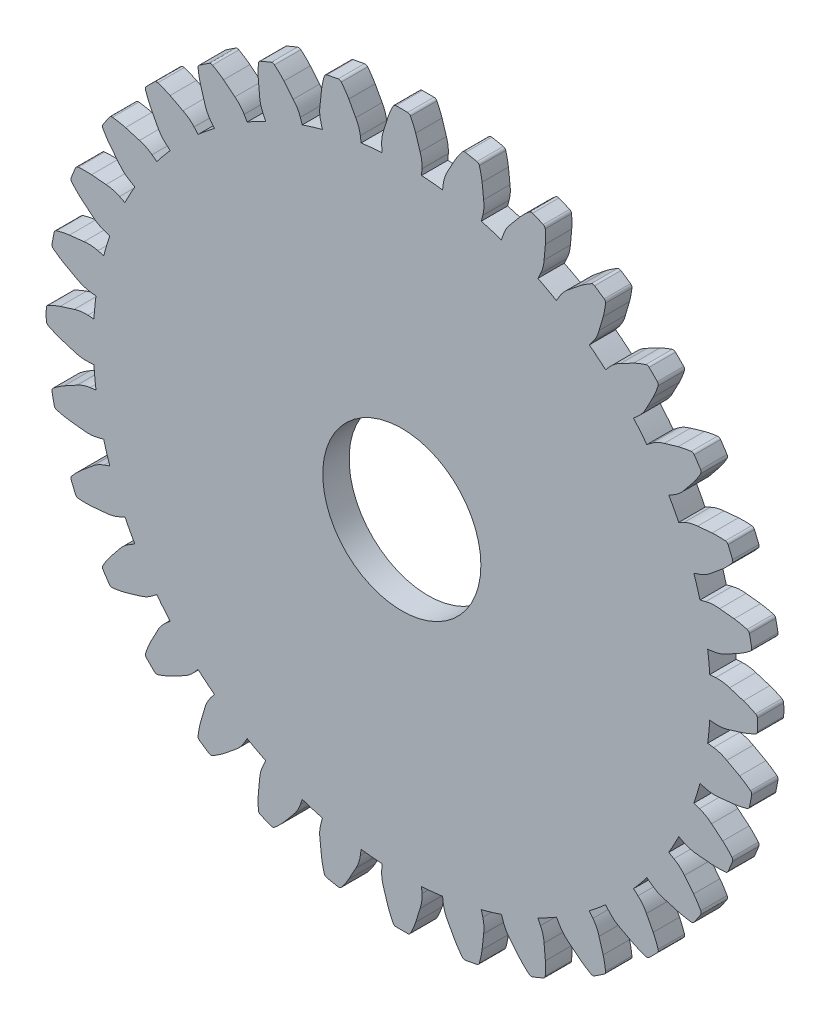
SolidWorks part; units mm, degrees
ref_plane "Front Plane" through (0, 0, 0) normal (0, 0, 1) x (1, 0, 0)
ref_plane "Top Plane" through (0, 0, 0) normal (0, 1, 0) x (1, 0, 0)
ref_plane "Right Plane" through (0, 0, 0) normal (1, 0, 0) x (0, 0, -1)
sketch "Model" plane through (0, 0, 0) normal (0, 0, 1) x (1, 0, 0)
  line L0 (51.5868, 30.5487) -> (52.0385, 30.5776)
  line L1 (51.5868, 27.5539) -> (52.0385, 27.525)
  line L2 (51.43, 25.9611) -> (51.8786, 25.9014)
  line L3 (50.8457, 23.0239) -> (51.283, 22.9074)
  line L4 (50.3811, 21.4923) -> (50.8094, 21.3462)
  line L5 (49.2351, 18.7255) -> (49.6412, 18.5259)
  line L6 (48.4806, 17.3139) -> (48.8722, 17.0871)
  line L7 (46.8168, 14.8239) -> (47.1762, 14.5489)
  line L8 (45.8014, 13.5867) -> (46.1412, 13.2878)
  line L9 (43.6838, 11.469) -> (43.9827, 11.1292)
  line L10 (42.4466, 10.4537) -> (42.7216, 10.0942)
  line L11 (39.9565, 8.7899) -> (40.1834, 8.3983)
  line L12 (38.545, 8.0354) -> (38.7446, 7.6292)
  line L13 (35.7782, 6.8893) -> (35.9243, 6.461)
  line L14 (34.2466, 6.4247) -> (34.3631, 5.9874)
  line L15 (31.3093, 5.8405) -> (31.3691, 5.3919)
  line L16 (29.7165, 5.6836) -> (29.7455, 5.232)
  line L17 (26.7218, 5.6836) -> (26.6928, 5.232)
  line L18 (25.1289, 5.8405) -> (25.0692, 5.3919)
  line L19 (22.1917, 6.4247) -> (22.0752, 5.9874)
  line L20 (20.6601, 6.8893) -> (20.514, 6.461)
  line L21 (17.8933, 8.0354) -> (17.6937, 7.6292)
  line L22 (16.4818, 8.7899) -> (16.2549, 8.3983)
  line L23 (13.9917, 10.4537) -> (13.7167, 10.0942)
  line L24 (12.7545, 11.469) -> (12.4556, 11.1292)
  line L25 (10.6369, 13.5867) -> (10.2971, 13.2878)
  line L26 (9.6215, 14.8239) -> (9.2621, 14.5489)
  line L27 (7.9577, 17.3139) -> (7.5661, 17.0871)
  line L28 (7.2032, 18.7255) -> (6.797, 18.5259)
  line L29 (6.0572, 21.4923) -> (5.6288, 21.3462)
  line L30 (5.5926, 23.0239) -> (5.1553, 22.9074)
  line L31 (5.0083, 25.9611) -> (4.5597, 25.9014)
  line L32 (4.8514, 27.5539) -> (4.3998, 27.525)
  line L33 (4.8514, 30.5487) -> (4.3998, 30.5776)
  line L34 (5.0083, 32.1415) -> (4.5597, 32.2012)
  line L35 (5.5926, 35.0787) -> (5.1553, 35.1952)
  line L36 (6.0572, 36.6103) -> (5.6288, 36.7564)
  line L37 (7.2032, 39.3771) -> (6.797, 39.5767)
  line L38 (7.9577, 40.7887) -> (7.5661, 41.0155)
  line L39 (9.6215, 43.2787) -> (9.2621, 43.5537)
  line L40 (10.6369, 44.516) -> (10.2971, 44.8148)
  line L41 (12.7545, 46.6336) -> (12.4556, 46.9734)
  line L42 (13.9917, 47.6489) -> (13.7167, 48.0084)
  line L43 (16.4818, 49.3127) -> (16.2549, 49.7043)
  line L44 (17.8933, 50.0672) -> (17.6937, 50.4734)
  line L45 (20.6601, 51.2133) -> (20.514, 51.6416)
  line L46 (22.1917, 51.6779) -> (22.0752, 52.1152)
  line L47 (25.1289, 52.2621) -> (25.0692, 52.7107)
  line L48 (26.7218, 52.419) -> (26.6928, 52.8706)
  line L49 (29.7165, 52.419) -> (29.7455, 52.8706)
  line L50 (31.3093, 52.2621) -> (31.3691, 52.7107)
  line L51 (34.2466, 51.6779) -> (34.3631, 52.1152)
  line L52 (35.7782, 51.2133) -> (35.9243, 51.6416)
  line L53 (38.545, 50.0672) -> (38.7446, 50.4734)
  line L54 (39.9565, 49.3127) -> (40.1834, 49.7043)
  line L55 (42.4466, 47.6489) -> (42.7216, 48.0084)
  line L56 (43.6838, 46.6336) -> (43.9827, 46.9734)
  line L57 (45.8014, 44.516) -> (46.1412, 44.8148)
  line L58 (46.8168, 43.2787) -> (47.1762, 43.5537)
  line L59 (48.4806, 40.7887) -> (48.8722, 41.0155)
  line L60 (49.2351, 39.3771) -> (49.6412, 39.5767)
  line L61 (50.3811, 36.6103) -> (50.8094, 36.7564)
  line L62 (50.8457, 35.0787) -> (51.283, 35.1952)
  line L63 (51.43, 32.1415) -> (51.8786, 32.2012)
  arc A0 (51.5868, 30.5487) -> (51.522, 31.3464) centre (28.2191, 29.0513) ccw
  arc A1 (53.0886, 30.435) -> (52.0385, 30.5776) centre (52.2099, 27.9016) ccw
  arc A2 (54.1454, 30.1056) -> (53.0886, 30.435) centre (-995.2612, -3334.4727) ccw
  arc A3 (55.2066, 29.0513) -> (55.203, 29.4932) centre (28.2191, 29.0513) ccw
  arc A4 (55.0676, 29.7109) -> (54.1454, 30.1056) centre (51.7985, 23.3471) ccw
  arc A5 (55.203, 29.4932) -> (55.0676, 29.7109) centre (54.9537, 29.4891) ccw
  arc A6 (51.522, 26.7562) -> (51.5868, 27.5539) centre (28.2191, 29.0513) ccw
  arc A7 (52.0385, 27.525) -> (53.0886, 27.6676) centre (52.2099, 30.201) ccw
  arc A8 (53.0886, 27.6676) -> (54.1454, 27.997) centre (-995.2612, 3392.5754) ccw
  arc A9 (55.203, 28.6094) -> (55.2066, 29.0513) centre (28.2191, 29.0513) ccw
  arc A10 (54.1454, 27.997) -> (55.0676, 28.3917) centre (51.7985, 34.7555) ccw
  arc A11 (55.0676, 28.3917) -> (55.203, 28.6094) centre (54.9537, 28.6135) ccw
  arc A12 (51.43, 25.9611) -> (51.522, 26.7562) centre (28.2191, 29.0513) ccw
  arc A13 (52.8807, 25.5567) -> (51.8786, 25.9014) centre (51.5246, 23.2433) ccw
  arc A14 (53.853, 25.0274) -> (52.8807, 25.5567) centre (-1631.7863, -3070.1725) ccw
  arc A15 (54.6881, 23.7863) -> (54.7708, 24.2204) centre (28.2191, 29.0513) ccw
  arc A16 (54.6804, 24.4604) -> (53.853, 25.0274) centre (50.2327, 18.8566) ccw
  arc A17 (54.7708, 24.2204) -> (54.6804, 24.4604) centre (54.5254, 24.2651) ccw
  arc A18 (50.6265, 22.2541) -> (50.8457, 23.0239) centre (28.2191, 29.0513) ccw
  arc A19 (51.283, 22.9074) -> (52.3408, 22.8424) centre (51.9732, 25.4985) ccw
  arc A20 (52.3408, 22.8424) -> (53.4416, 22.9593) centre (-319.4043, 3527.6173) ccw
  arc A21 (54.5983, 23.3536) -> (54.6881, 23.7863) centre (28.2191, 29.0513) ccw
  arc A22 (53.4416, 22.9593) -> (54.4231, 23.1665) centre (52.4583, 30.0457) ccw
  arc A23 (54.4231, 23.1665) -> (54.5983, 23.3536) centre (54.3546, 23.4062) ccw
  arc A24 (50.3811, 21.4923) -> (50.6265, 22.2541) centre (28.2191, 29.0513) ccw
  arc A25 (51.7251, 20.8126) -> (50.8094, 21.3462) centre (49.9437, 18.8083) ccw
  arc A26 (52.5754, 20.1038) -> (51.7251, 20.8126) centre (-2204.5183, -2686.7708) ccw
  arc A27 (53.1523, 18.7236) -> (53.3181, 19.1333) centre (28.2191, 29.0513) ccw
  arc A28 (53.2764, 19.3862) -> (52.5754, 20.1038) centre (47.8208, 14.7579) ccw
  arc A29 (53.3181, 19.1333) -> (53.2764, 19.3862) centre (53.0862, 19.2249) ccw
  arc A30 (48.8699, 18.0133) -> (49.2351, 18.7255) centre (28.2191, 29.0513) ccw
  arc A31 (49.6412, 18.5259) -> (50.666, 18.2558) centre (50.8237, 20.9326) ccw
  arc A32 (50.666, 18.2558) -> (51.7685, 18.1557) centre (369.8115, 3528.2113) ccw
  arc A33 (52.9799, 18.3168) -> (53.1523, 18.7236) centre (28.2191, 29.0513) ccw
  arc A34 (51.7685, 18.1557) -> (52.7715, 18.1674) centre (52.1866, 25.2978) ccw
  arc A35 (52.7715, 18.1674) -> (52.9799, 18.3168) centre (52.7511, 18.4159) ccw
  arc A36 (48.4806, 17.3139) -> (48.8699, 18.0133) centre (28.2191, 29.0513) ccw
  arc A37 (49.6661, 16.3851) -> (48.8722, 17.0871) centre (47.528, 14.7668) ccw
  arc A38 (50.3618, 15.524) -> (49.6661, 16.3851) centre (-2691.4475, -2199.0015) ccw
  arc A39 (50.6584, 14.0579) -> (50.9009, 14.4273) centre (28.2191, 29.0513) ccw
  arc A40 (50.9093, 14.6835) -> (50.3618, 15.524) centre (44.6556, 11.2085) ccw
  arc A41 (50.9009, 14.4273) -> (50.9093, 14.6835) centre (50.6914, 14.5624) ccw
  arc A42 (46.3197, 14.1966) -> (46.8168, 14.8239) centre (28.2191, 29.0513) ccw
  arc A43 (47.1762, 14.5489) -> (48.1286, 14.084) centre (48.8055, 16.6787) ccw
  arc A44 (48.1286, 14.084) -> (49.1903, 13.7708) centre (1045.9002, 3394.3346) ccw
  arc A45 (50.4099, 13.6924) -> (50.6584, 14.0579) centre (28.2191, 29.0513) ccw
  arc A46 (49.1903, 13.7708) -> (50.1764, 13.5866) centre (50.9938, 20.6941) ccw
  arc A47 (50.1764, 13.5866) -> (50.4099, 13.6924) centre (50.2049, 13.8344) ccw
  arc A48 (45.8014, 13.5867) -> (46.3197, 14.1966) centre (28.2191, 29.0513) ccw
  arc A49 (46.783, 12.4444) -> (46.1412, 13.2878) centre (44.3702, 11.2743) ccw
  arc A50 (47.2973, 11.4641) -> (46.783, 12.4444) centre (-3073.8614, -1625.6095) ccw
  arc A51 (47.3022, 9.9683) -> (47.6121, 10.2833) centre (28.2191, 29.0513) ccw
  arc A52 (47.6703, 10.533) -> (47.2973, 11.4641) centre (40.8589, 8.3447) ccw
  arc A53 (47.6121, 10.2833) -> (47.6703, 10.533) centre (47.4329, 10.4567) ccw
  arc A54 (43.0739, 10.9508) -> (43.6838, 11.469) centre (28.2191, 29.0513) ccw
  arc A55 (43.9827, 11.1292) -> (44.8261, 10.4875) centre (45.9961, 12.9002) ccw
  arc A56 (44.8261, 10.4875) -> (45.8063, 9.9731) centre (1682.8799, 3131.1319) ccw
  arc A57 (46.9872, 9.6583) -> (47.3022, 9.9683) centre (28.2191, 29.0513) ccw
  arc A58 (45.8063, 9.9731) -> (46.7375, 9.6001) centre (48.9258, 16.4116) ccw
  arc A59 (46.7375, 9.6001) -> (46.9872, 9.6583) centre (46.8137, 9.8375) ccw
  arc A60 (42.4466, 10.4537) -> (43.0739, 10.9508) centre (28.2191, 29.0513) ccw
  arc A61 (43.1864, 9.1418) -> (42.7216, 10.0942) centre (40.5918, 8.465) ccw
  arc A62 (43.4996, 8.0801) -> (43.1864, 9.1418) centre (-3337.0641, -988.6297) ccw
  arc A63 (43.2126, 6.612) -> (43.578, 6.8605) centre (28.2191, 29.0513) ccw
  arc A64 (43.6838, 7.0941) -> (43.4996, 8.0801) centre (36.5763, 6.2767) ccw
  arc A65 (43.578, 6.8605) -> (43.6838, 7.0941) centre (43.4361, 7.0656) ccw
  arc A66 (39.2572, 8.4006) -> (39.9565, 8.7899) centre (28.2191, 29.0513) ccw
  arc A67 (40.1834, 8.3983) -> (40.8854, 7.6043) centre (42.5036, 9.7425) ccw
  arc A68 (40.8854, 7.6043) -> (41.7464, 6.9086) centre (2256.272, 2748.7179) ccw
  arc A69 (42.8432, 6.3695) -> (43.2126, 6.612) centre (28.2191, 29.0513) ccw
  arc A70 (41.7464, 6.9086) -> (42.5869, 6.3611) centre (46.062, 12.6148) ccw
  arc A71 (42.5869, 6.3611) -> (42.8432, 6.3695) centre (42.708, 6.5791) ccw
  arc A72 (38.545, 8.0354) -> (39.2572, 8.4006) centre (28.2191, 29.0513) ccw
  arc A73 (39.0147, 6.6044) -> (38.7446, 7.6292) centre (36.3378, 6.4468) ccw
  arc A74 (39.1148, 5.502) -> (39.0147, 6.6044) centre (-3470.9409, -312.5411) ccw
  arc A75 (38.5468, 4.1181) -> (38.9537, 4.2906) centre (28.2191, 29.0513) ccw
  arc A76 (39.103, 4.499) -> (39.1148, 5.502) centre (31.9726, 5.0839) ccw
  arc A77 (38.9537, 4.2906) -> (39.103, 4.499) centre (38.8545, 4.5193) ccw
  arc A78 (35.0163, 6.6439) -> (35.7782, 6.8893) centre (28.2191, 29.0513) ccw
  arc A79 (35.9243, 6.461) -> (36.4579, 5.5454) centre (38.4622, 7.3267) ccw
  arc A80 (36.4579, 5.5454) -> (37.1667, 4.6951) centre (2744.0412, 2261.7888) ccw
  arc A81 (38.1372, 3.9523) -> (38.5468, 4.1181) centre (28.2191, 29.0513) ccw
  arc A82 (37.1667, 4.6951) -> (37.8842, 3.9941) centre (42.5125, 9.4497) ccw
  arc A83 (37.8842, 3.9941) -> (38.1372, 3.9523) centre (38.0455, 4.1843) ccw
  arc A84 (34.2466, 6.4247) -> (35.0163, 6.6439) centre (28.2191, 29.0513) ccw
  arc A85 (34.4281, 4.9296) -> (34.3631, 5.9874) centre (31.7719, 5.2972) ccw
  arc A86 (34.3112, 3.8289) -> (34.4281, 4.9296) centre (-3470.3468, 376.6748) ccw
  arc A87 (33.4841, 2.5824) -> (33.9169, 2.6721) centre (28.2191, 29.0513) ccw
  arc A88 (34.104, 2.8474) -> (34.3112, 3.8289) centre (27.2247, 4.8121) ccw
  arc A89 (33.9169, 2.6721) -> (34.104, 2.8474) centre (33.8642, 2.9159) ccw
  arc A90 (30.5143, 5.7484) -> (31.3093, 5.8405) centre (28.2191, 29.0513) ccw
  arc A91 (31.3691, 5.3919) -> (31.7138, 4.3897) centre (34.0271, 5.7458) ccw
  arc A92 (31.7138, 4.3897) -> (32.2431, 3.4175) centre (3127.4429, 1689.0567) ccw
  arc A93 (33.05, 2.4997) -> (33.4841, 2.5824) centre (28.2191, 29.0513) ccw
  arc A94 (32.2431, 3.4175) -> (32.8101, 2.59) centre (38.4138, 7.0378) ccw
  arc A95 (32.8101, 2.59) -> (33.05, 2.4997) centre (33.0054, 2.745) ccw
  arc A96 (29.7165, 5.6836) -> (30.5143, 5.7484) centre (28.2191, 29.0513) ccw
  arc A97 (29.6029, 4.1818) -> (29.7455, 5.232) centre (27.0695, 5.0606) ccw
  arc A98 (29.2734, 3.125) -> (29.6029, 4.1818) centre (-3335.3049, 1052.5316) ccw
  arc A99 (28.2191, 2.0638) -> (28.661, 2.0674) centre (28.2191, 29.0513) ccw
  arc A100 (28.8788, 2.2028) -> (29.2734, 3.125) centre (22.515, 5.4719) ccw
  arc A101 (28.661, 2.0674) -> (28.8788, 2.2028) centre (28.657, 2.3168) ccw
  arc A102 (25.924, 5.7484) -> (26.7218, 5.6836) centre (28.2191, 29.0513) ccw
  arc A103 (26.6928, 5.232) -> (26.8354, 4.1818) centre (29.3688, 5.0606) ccw
  arc A104 (26.8354, 4.1818) -> (27.1648, 3.125) centre (3391.7432, 1052.5316) ccw
  arc A105 (27.7772, 2.0674) -> (28.2191, 2.0638) centre (28.2191, 29.0513) ccw
  arc A106 (27.1648, 3.125) -> (27.5595, 2.2028) centre (33.9233, 5.4719) ccw
  arc A107 (27.5595, 2.2028) -> (27.7772, 2.0674) centre (27.7813, 2.3168) ccw
  arc A108 (25.1289, 5.8405) -> (25.924, 5.7484) centre (28.2191, 29.0513) ccw
  arc A109 (24.7245, 4.3897) -> (25.0692, 5.3919) centre (22.4112, 5.7458) ccw
  arc A110 (24.1952, 3.4175) -> (24.7245, 4.3897) centre (-3071.0046, 1689.0567) ccw
  arc A111 (22.9541, 2.5824) -> (23.3883, 2.4997) centre (28.2191, 29.0513) ccw
  arc A112 (23.6282, 2.59) -> (24.1952, 3.4175) centre (18.0245, 7.0378) ccw
  arc A113 (23.3883, 2.4997) -> (23.6282, 2.59) centre (23.4329, 2.745) ccw
  arc A114 (21.4219, 6.6439) -> (22.1917, 6.4247) centre (28.2191, 29.0513) ccw
  arc A115 (22.0752, 5.9874) -> (22.0102, 4.9296) centre (24.6664, 5.2972) ccw
  arc A116 (22.0102, 4.9296) -> (22.1271, 3.8289) centre (3526.7851, 376.6748) ccw
  arc A117 (22.5214, 2.6721) -> (22.9541, 2.5824) centre (28.2191, 29.0513) ccw
  arc A118 (22.1271, 3.8289) -> (22.3343, 2.8474) centre (29.2136, 4.8121) ccw
  arc A119 (22.3343, 2.8474) -> (22.5214, 2.6721) centre (22.5741, 2.9159) ccw
  arc A120 (20.6601, 6.8893) -> (21.4219, 6.6439) centre (28.2191, 29.0513) ccw
  arc A121 (19.9804, 5.5454) -> (20.514, 6.461) centre (17.9761, 7.3267) ccw
  arc A122 (19.2716, 4.6951) -> (19.9804, 5.5454) centre (-2687.6029, 2261.7888) ccw
  arc A123 (17.8915, 4.1181) -> (18.3011, 3.9523) centre (28.2191, 29.0513) ccw
  arc A124 (18.5541, 3.9941) -> (19.2716, 4.6951) centre (13.9257, 9.4497) ccw
  arc A125 (18.3011, 3.9523) -> (18.5541, 3.9941) centre (18.3928, 4.1843) ccw
  arc A126 (17.1811, 8.4006) -> (17.8933, 8.0354) centre (28.2191, 29.0513) ccw
  arc A127 (17.6937, 7.6292) -> (17.4236, 6.6044) centre (20.1005, 6.4468) ccw
  arc A128 (17.4236, 6.6044) -> (17.3235, 5.502) centre (3527.3791, -312.5411) ccw
  arc A129 (17.4846, 4.2906) -> (17.8915, 4.1181) centre (28.2191, 29.0513) ccw
  arc A130 (17.3235, 5.502) -> (17.3353, 4.499) centre (24.4657, 5.0839) ccw
  arc A131 (17.3353, 4.499) -> (17.4846, 4.2906) centre (17.5838, 4.5193) ccw
  arc A132 (16.4818, 8.7899) -> (17.1811, 8.4006) centre (28.2191, 29.0513) ccw
  arc A133 (15.5529, 7.6043) -> (16.2549, 8.3983) centre (13.9347, 9.7425) ccw
  arc A134 (14.6919, 6.9086) -> (15.5529, 7.6043) centre (-2199.8337, 2748.7179) ccw
  arc A135 (13.2257, 6.612) -> (13.5951, 6.3695) centre (28.2191, 29.0513) ccw
  arc A136 (13.8514, 6.3611) -> (14.6919, 6.9086) centre (10.3763, 12.6148) ccw
  arc A137 (13.5951, 6.3695) -> (13.8514, 6.3611) centre (13.7303, 6.5791) ccw
  arc A138 (13.3644, 10.9508) -> (13.9917, 10.4537) centre (28.2191, 29.0513) ccw
  arc A139 (13.7167, 10.0942) -> (13.2519, 9.1418) centre (15.8465, 8.465) ccw
  arc A140 (13.2519, 9.1418) -> (12.9386, 8.0801) centre (3393.5024, -988.6297) ccw
  arc A141 (12.8603, 6.8605) -> (13.2257, 6.612) centre (28.2191, 29.0513) ccw
  arc A142 (12.9386, 8.0801) -> (12.7545, 7.0941) centre (19.862, 6.2767) ccw
  arc A143 (12.7545, 7.0941) -> (12.8603, 6.8605) centre (13.0022, 7.0656) ccw
  arc A144 (12.7545, 11.469) -> (13.3644, 10.9508) centre (28.2191, 29.0513) ccw
  arc A145 (11.6122, 10.4875) -> (12.4556, 11.1292) centre (10.4422, 12.9002) ccw
  arc A146 (10.632, 9.9731) -> (11.6122, 10.4875) centre (-1626.4416, 3131.1319) ccw
  arc A147 (9.1361, 9.9683) -> (9.4511, 9.6583) centre (28.2191, 29.0513) ccw
  arc A148 (9.7008, 9.6001) -> (10.632, 9.9731) centre (7.5125, 16.4116) ccw
  arc A149 (9.4511, 9.6583) -> (9.7008, 9.6001) centre (9.6245, 9.8375) ccw
  arc A150 (10.1186, 14.1966) -> (10.6369, 13.5867) centre (28.2191, 29.0513) ccw
  arc A151 (10.2971, 13.2878) -> (9.6553, 12.4444) centre (12.0681, 11.2743) ccw
  arc A152 (9.6553, 12.4444) -> (9.141, 11.4641) centre (3130.2997, -1625.6095) ccw
  arc A153 (8.8262, 10.2833) -> (9.1361, 9.9683) centre (28.2191, 29.0513) ccw
  arc A154 (9.141, 11.4641) -> (8.768, 10.533) centre (15.5794, 8.3447) ccw
  arc A155 (8.768, 10.533) -> (8.8262, 10.2833) centre (9.0054, 10.4567) ccw
  arc A156 (9.6215, 14.8239) -> (10.1186, 14.1966) centre (28.2191, 29.0513) ccw
  arc A157 (8.3097, 14.084) -> (9.2621, 14.5489) centre (7.6328, 16.6787) ccw
  arc A158 (7.248, 13.7708) -> (8.3097, 14.084) centre (-989.4619, 3394.3346) ccw
  arc A159 (5.7799, 14.0579) -> (6.0284, 13.6924) centre (28.2191, 29.0513) ccw
  arc A160 (6.2619, 13.5866) -> (7.248, 13.7708) centre (5.4445, 20.6941) ccw
  arc A161 (6.0284, 13.6924) -> (6.2619, 13.5866) centre (6.2334, 13.8344) ccw
  arc A162 (7.5684, 18.0133) -> (7.9577, 17.3139) centre (28.2191, 29.0513) ccw
  arc A163 (7.5661, 17.0871) -> (6.7722, 16.3851) centre (8.9103, 14.7668) ccw
  arc A164 (6.7722, 16.3851) -> (6.0765, 15.524) centre (2747.8858, -2199.0015) ccw
  arc A165 (5.5374, 14.4273) -> (5.7799, 14.0579) centre (28.2191, 29.0513) ccw
  arc A166 (6.0765, 15.524) -> (5.529, 14.6835) centre (11.7827, 11.2085) ccw
  arc A167 (5.529, 14.6835) -> (5.5374, 14.4273) centre (5.7469, 14.5624) ccw
  arc A168 (7.2032, 18.7255) -> (7.5684, 18.0133) centre (28.2191, 29.0513) ccw
  arc A169 (5.7723, 18.2558) -> (6.797, 18.5259) centre (5.6146, 20.9326) ccw
  arc A170 (4.6698, 18.1557) -> (5.7723, 18.2558) centre (-313.3732, 3528.2113) ccw
  arc A171 (3.2859, 18.7236) -> (3.4584, 18.3168) centre (28.2191, 29.0513) ccw
  arc A172 (3.6668, 18.1674) -> (4.6698, 18.1557) centre (4.2517, 25.2978) ccw
  arc A173 (3.4584, 18.3168) -> (3.6668, 18.1674) centre (3.6872, 18.4159) ccw
  arc A174 (5.8118, 22.2541) -> (6.0572, 21.4923) centre (28.2191, 29.0513) ccw
  arc A175 (5.6288, 21.3462) -> (4.7132, 20.8126) centre (6.4945, 18.8083) ccw
  arc A176 (4.7132, 20.8126) -> (3.8629, 20.1038) centre (2260.9566, -2686.7708) ccw
  arc A177 (3.1202, 19.1333) -> (3.2859, 18.7236) centre (28.2191, 29.0513) ccw
  arc A178 (3.8629, 20.1038) -> (3.1619, 19.3862) centre (8.6175, 14.7579) ccw
  arc A179 (3.1619, 19.3862) -> (3.1202, 19.1333) centre (3.3521, 19.2249) ccw
  arc A180 (5.5926, 23.0239) -> (5.8118, 22.2541) centre (28.2191, 29.0513) ccw
  arc A181 (4.0975, 22.8424) -> (5.1553, 22.9074) centre (4.4651, 25.4985) ccw
  arc A182 (2.9967, 22.9593) -> (4.0975, 22.8424) centre (375.8426, 3527.6173) ccw
  arc A183 (1.7502, 23.7863) -> (1.84, 23.3536) centre (28.2191, 29.0513) ccw
  arc A184 (2.0152, 23.1665) -> (2.9967, 22.9593) centre (3.98, 30.0457) ccw
  arc A185 (1.84, 23.3536) -> (2.0152, 23.1665) centre (2.0837, 23.4062) ccw
  arc A186 (4.9163, 26.7562) -> (5.0083, 25.9611) centre (28.2191, 29.0513) ccw
  arc A187 (4.5597, 25.9014) -> (3.5576, 25.5567) centre (4.9137, 23.2433) ccw
  arc A188 (3.5576, 25.5567) -> (2.5853, 25.0274) centre (1688.2246, -3070.1725) ccw
  arc A189 (1.6675, 24.2204) -> (1.7502, 23.7863) centre (28.2191, 29.0513) ccw
  arc A190 (2.5853, 25.0274) -> (1.7579, 24.4604) centre (6.2056, 18.8566) ccw
  arc A191 (1.7579, 24.4604) -> (1.6675, 24.2204) centre (1.9129, 24.2651) ccw
  arc A192 (4.8514, 27.5539) -> (4.9163, 26.7562) centre (28.2191, 29.0513) ccw
  arc A193 (3.3497, 27.6676) -> (4.3998, 27.525) centre (4.2284, 30.201) ccw
  arc A194 (2.2928, 27.997) -> (3.3497, 27.6676) centre (1051.6995, 3392.5754) ccw
  arc A195 (1.2316, 29.0513) -> (1.2353, 28.6094) centre (28.2191, 29.0513) ccw
  arc A196 (1.3707, 28.3917) -> (2.2928, 27.997) centre (4.6397, 34.7555) ccw
  arc A197 (1.2353, 28.6094) -> (1.3707, 28.3917) centre (1.4846, 28.6135) ccw
  arc A198 (4.9163, 31.3464) -> (4.8514, 30.5487) centre (28.2191, 29.0513) ccw
  arc A199 (4.3998, 30.5776) -> (3.3497, 30.435) centre (4.2284, 27.9016) ccw
  arc A200 (3.3497, 30.435) -> (2.2928, 30.1056) centre (1051.6995, -3334.4727) ccw
  arc A201 (1.2353, 29.4932) -> (1.2316, 29.0513) centre (28.2191, 29.0513) ccw
  arc A202 (2.2928, 30.1056) -> (1.3707, 29.7109) centre (4.6397, 23.3471) ccw
  arc A203 (1.3707, 29.7109) -> (1.2353, 29.4932) centre (1.4846, 29.4891) ccw
  arc A204 (5.0083, 32.1415) -> (4.9163, 31.3464) centre (28.2191, 29.0513) ccw
  arc A205 (3.5576, 32.546) -> (4.5597, 32.2012) centre (4.9137, 34.8593) ccw
  arc A206 (2.5853, 33.0752) -> (3.5576, 32.546) centre (1688.2246, 3128.2751) ccw
  arc A207 (1.7502, 34.3163) -> (1.6675, 33.8822) centre (28.2191, 29.0513) ccw
  arc A208 (1.7579, 33.6422) -> (2.5853, 33.0752) centre (6.2056, 39.246) ccw
  arc A209 (1.6675, 33.8822) -> (1.7579, 33.6422) centre (1.9129, 33.8376) ccw
  arc A210 (5.8118, 35.8485) -> (5.5926, 35.0787) centre (28.2191, 29.0513) ccw
  arc A211 (5.1553, 35.1952) -> (4.0975, 35.2603) centre (4.4651, 32.6041) ccw
  arc A212 (4.0975, 35.2603) -> (2.9967, 35.1433) centre (375.8426, -3469.5147) ccw
  arc A213 (1.84, 34.749) -> (1.7502, 34.3163) centre (28.2191, 29.0513) ccw
  arc A214 (2.9967, 35.1433) -> (2.0152, 34.9361) centre (3.98, 28.0569) ccw
  arc A215 (2.0152, 34.9361) -> (1.84, 34.749) centre (2.0837, 34.6964) ccw
  arc A216 (6.0572, 36.6103) -> (5.8118, 35.8485) centre (28.2191, 29.0513) ccw
  arc A217 (4.7132, 37.29) -> (5.6288, 36.7564) centre (6.4945, 39.2943) ccw
  arc A218 (3.8629, 37.9988) -> (4.7132, 37.29) centre (2260.9566, 2744.8734) ccw
  arc A219 (3.2859, 39.379) -> (3.1202, 38.9693) centre (28.2191, 29.0513) ccw
  arc A220 (3.1619, 38.7164) -> (3.8629, 37.9988) centre (8.6175, 43.3447) ccw
  arc A221 (3.1202, 38.9693) -> (3.1619, 38.7164) centre (3.3521, 38.8777) ccw
  arc A222 (7.5684, 40.0894) -> (7.2032, 39.3771) centre (28.2191, 29.0513) ccw
  arc A223 (6.797, 39.5767) -> (5.7723, 39.8469) centre (5.6146, 37.17) ccw
  arc A224 (5.7723, 39.8469) -> (4.6698, 39.9469) centre (-313.3732, -3470.1087) ccw
  arc A225 (3.4584, 39.7859) -> (3.2859, 39.379) centre (28.2191, 29.0513) ccw
  arc A226 (4.6698, 39.9469) -> (3.6668, 39.9352) centre (4.2517, 32.8048) ccw
  arc A227 (3.6668, 39.9352) -> (3.4584, 39.7859) centre (3.6872, 39.6867) ccw
  arc A228 (7.9577, 40.7887) -> (7.5684, 40.0894) centre (28.2191, 29.0513) ccw
  arc A229 (6.7722, 41.7175) -> (7.5661, 41.0155) centre (8.9103, 43.3358) ccw
  arc A230 (6.0765, 42.5786) -> (6.7722, 41.7175) centre (2747.8858, 2257.1041) ccw
  arc A231 (5.7799, 44.0448) -> (5.5374, 43.6753) centre (28.2191, 29.0513) ccw
  arc A232 (5.529, 43.4191) -> (6.0765, 42.5786) centre (11.7827, 46.8942) ccw
  arc A233 (5.5374, 43.6753) -> (5.529, 43.4191) centre (5.7469, 43.5402) ccw
  arc A234 (10.1186, 43.906) -> (9.6215, 43.2787) centre (28.2191, 29.0513) ccw
  arc A235 (9.2621, 43.5537) -> (8.3097, 44.0186) centre (7.6328, 41.4239) ccw
  arc A236 (8.3097, 44.0186) -> (7.248, 44.3318) centre (-989.4619, -3336.2319) ccw
  arc A237 (6.0284, 44.4102) -> (5.7799, 44.0448) centre (28.2191, 29.0513) ccw
  arc A238 (7.248, 44.3318) -> (6.2619, 44.516) centre (5.4445, 37.4085) ccw
  arc A239 (6.2619, 44.516) -> (6.0284, 44.4102) centre (6.2334, 44.2683) ccw
  arc A240 (10.6369, 44.516) -> (10.1186, 43.906) centre (28.2191, 29.0513) ccw
  arc A241 (9.6553, 45.6582) -> (10.2971, 44.8148) centre (12.0681, 46.8283) ccw
  arc A242 (9.141, 46.6385) -> (9.6553, 45.6582) centre (3130.2997, 1683.7121) ccw
  arc A243 (9.1361, 48.1343) -> (8.8262, 47.8193) centre (28.2191, 29.0513) ccw
  arc A244 (8.768, 47.5696) -> (9.141, 46.6385) centre (15.5794, 49.7579) ccw
  arc A245 (8.8262, 47.8193) -> (8.768, 47.5696) centre (9.0054, 47.6459) ccw
  arc A246 (13.3644, 47.1518) -> (12.7545, 46.6336) centre (28.2191, 29.0513) ccw
  arc A247 (12.4556, 46.9734) -> (11.6122, 47.6151) centre (10.4422, 45.2024) ccw
  arc A248 (11.6122, 47.6151) -> (10.632, 48.1295) centre (-1626.4416, -3073.0293) ccw
  arc A249 (9.4511, 48.4443) -> (9.1361, 48.1343) centre (28.2191, 29.0513) ccw
  arc A250 (10.632, 48.1295) -> (9.7008, 48.5025) centre (7.5125, 41.691) ccw
  arc A251 (9.7008, 48.5025) -> (9.4511, 48.4443) centre (9.6245, 48.2651) ccw
  arc A252 (13.9917, 47.6489) -> (13.3644, 47.1518) centre (28.2191, 29.0513) ccw
  arc A253 (13.2519, 48.9608) -> (13.7167, 48.0084) centre (15.8465, 49.6376) ccw
  arc A254 (12.9386, 50.0225) -> (13.2519, 48.9608) centre (3393.5024, 1046.7323) ccw
  arc A255 (13.2257, 51.4906) -> (12.8603, 51.2421) centre (28.2191, 29.0513) ccw
  arc A256 (12.7545, 51.0085) -> (12.9386, 50.0225) centre (19.862, 51.8259) ccw
  arc A257 (12.8603, 51.2421) -> (12.7545, 51.0085) centre (13.0022, 51.037) ccw
  arc A258 (17.1811, 49.702) -> (16.4818, 49.3127) centre (28.2191, 29.0513) ccw
  arc A259 (16.2549, 49.7043) -> (15.5529, 50.4983) centre (13.9347, 48.3602) ccw
  arc A260 (15.5529, 50.4983) -> (14.6919, 51.194) centre (-2199.8337, -2690.6153) ccw
  arc A261 (13.5951, 51.7331) -> (13.2257, 51.4906) centre (28.2191, 29.0513) ccw
  arc A262 (14.6919, 51.194) -> (13.8514, 51.7415) centre (10.3763, 45.4878) ccw
  arc A263 (13.8514, 51.7415) -> (13.5951, 51.7331) centre (13.7303, 51.5235) ccw
  arc A264 (17.8933, 50.0672) -> (17.1811, 49.702) centre (28.2191, 29.0513) ccw
  arc A265 (17.4236, 51.4982) -> (17.6937, 50.4734) centre (20.1005, 51.6558) ccw
  arc A266 (17.3235, 52.6006) -> (17.4236, 51.4982) centre (3527.3791, 370.6437) ccw
  arc A267 (17.8915, 53.9845) -> (17.4846, 53.8121) centre (28.2191, 29.0513) ccw
  arc A268 (17.3353, 53.6037) -> (17.3235, 52.6006) centre (24.4657, 53.0187) ccw
  arc A269 (17.4846, 53.8121) -> (17.3353, 53.6037) centre (17.5838, 53.5833) ccw
  arc A270 (21.4219, 51.4587) -> (20.6601, 51.2133) centre (28.2191, 29.0513) ccw
  arc A271 (20.514, 51.6416) -> (19.9804, 52.5573) centre (17.9761, 50.7759) ccw
  arc A272 (19.9804, 52.5573) -> (19.2716, 53.4075) centre (-2687.6029, -2203.6862) ccw
  arc A273 (18.3011, 54.1503) -> (17.8915, 53.9845) centre (28.2191, 29.0513) ccw
  arc A274 (19.2716, 53.4075) -> (18.5541, 54.1085) centre (13.9257, 48.6529) ccw
  arc A275 (18.5541, 54.1085) -> (18.3011, 54.1503) centre (18.3928, 53.9184) ccw
  arc A276 (22.1917, 51.6779) -> (21.4219, 51.4587) centre (28.2191, 29.0513) ccw
  arc A277 (22.0102, 53.173) -> (22.0752, 52.1152) centre (24.6664, 52.8054) ccw
  arc A278 (22.1271, 54.2738) -> (22.0102, 53.173) centre (3526.7851, -318.5722) ccw
  arc A279 (22.9541, 55.5202) -> (22.5214, 55.4305) centre (28.2191, 29.0513) ccw
  arc A280 (22.3343, 55.2552) -> (22.1271, 54.2738) centre (29.2136, 53.2905) ccw
  arc A281 (22.5214, 55.4305) -> (22.3343, 55.2552) centre (22.5741, 55.1867) ccw
  arc A282 (25.924, 52.3542) -> (25.1289, 52.2621) centre (28.2191, 29.0513) ccw
  arc A283 (25.0692, 52.7107) -> (24.7245, 53.7129) centre (22.4112, 52.3568) ccw
  arc A284 (24.7245, 53.7129) -> (24.1952, 54.6851) centre (-3071.0046, -1630.9541) ccw
  arc A285 (23.3883, 55.6029) -> (22.9541, 55.5202) centre (28.2191, 29.0513) ccw
  arc A286 (24.1952, 54.6851) -> (23.6282, 55.5126) centre (18.0245, 51.0648) ccw
  arc A287 (23.6282, 55.5126) -> (23.3883, 55.6029) centre (23.4329, 55.3576) ccw
  arc A288 (26.7218, 52.419) -> (25.924, 52.3542) centre (28.2191, 29.0513) ccw
  arc A289 (26.8354, 53.9208) -> (26.6928, 52.8706) centre (29.3688, 53.0421) ccw
  arc A290 (27.1648, 54.9776) -> (26.8354, 53.9208) centre (3391.7432, -994.429) ccw
  arc A291 (28.2191, 56.0388) -> (27.7772, 56.0352) centre (28.2191, 29.0513) ccw
  arc A292 (27.5595, 55.8998) -> (27.1648, 54.9776) centre (33.9233, 52.6307) ccw
  arc A293 (27.7772, 56.0352) -> (27.5595, 55.8998) centre (27.7813, 55.7859) ccw
  arc A294 (30.5143, 52.3542) -> (29.7165, 52.419) centre (28.2191, 29.0513) ccw
  arc A295 (29.7455, 52.8706) -> (29.6029, 53.9208) centre (27.0695, 53.0421) ccw
  arc A296 (29.6029, 53.9208) -> (29.2734, 54.9776) centre (-3335.3049, -994.429) ccw
  arc A297 (28.661, 56.0352) -> (28.2191, 56.0388) centre (28.2191, 29.0513) ccw
  arc A298 (29.2734, 54.9776) -> (28.8788, 55.8998) centre (22.515, 52.6307) ccw
  arc A299 (28.8788, 55.8998) -> (28.661, 56.0352) centre (28.657, 55.7859) ccw
  arc A300 (31.3093, 52.2621) -> (30.5143, 52.3542) centre (28.2191, 29.0513) ccw
  arc A301 (31.7138, 53.7129) -> (31.3691, 52.7107) centre (34.0271, 52.3568) ccw
  arc A302 (32.2431, 54.6851) -> (31.7138, 53.7129) centre (3127.4429, -1630.9541) ccw
  arc A303 (33.4841, 55.5202) -> (33.05, 55.6029) centre (28.2191, 29.0513) ccw
  arc A304 (32.8101, 55.5126) -> (32.2431, 54.6851) centre (38.4138, 51.0648) ccw
  arc A305 (33.05, 55.6029) -> (32.8101, 55.5126) centre (33.0054, 55.3576) ccw
  arc A306 (35.0163, 51.4587) -> (34.2466, 51.6779) centre (28.2191, 29.0513) ccw
  arc A307 (34.3631, 52.1152) -> (34.4281, 53.173) centre (31.7719, 52.8054) ccw
  arc A308 (34.4281, 53.173) -> (34.3112, 54.2738) centre (-3470.3468, -318.5722) ccw
  arc A309 (33.9169, 55.4305) -> (33.4841, 55.5202) centre (28.2191, 29.0513) ccw
  arc A310 (34.3112, 54.2738) -> (34.104, 55.2552) centre (27.2247, 53.2905) ccw
  arc A311 (34.104, 55.2552) -> (33.9169, 55.4305) centre (33.8642, 55.1867) ccw
  arc A312 (35.7782, 51.2133) -> (35.0163, 51.4587) centre (28.2191, 29.0513) ccw
  arc A313 (36.4579, 52.5573) -> (35.9243, 51.6416) centre (38.4622, 50.7759) ccw
  arc A314 (37.1667, 53.4075) -> (36.4579, 52.5573) centre (2744.0412, -2203.6862) ccw
  arc A315 (38.5468, 53.9845) -> (38.1372, 54.1503) centre (28.2191, 29.0513) ccw
  arc A316 (37.8842, 54.1085) -> (37.1667, 53.4075) centre (42.5125, 48.6529) ccw
  arc A317 (38.1372, 54.1503) -> (37.8842, 54.1085) centre (38.0455, 53.9184) ccw
  arc A318 (39.2572, 49.702) -> (38.545, 50.0672) centre (28.2191, 29.0513) ccw
  arc A319 (38.7446, 50.4734) -> (39.0147, 51.4982) centre (36.3378, 51.6558) ccw
  arc A320 (39.0147, 51.4982) -> (39.1148, 52.6006) centre (-3470.9409, 370.6437) ccw
  arc A321 (38.9537, 53.8121) -> (38.5468, 53.9845) centre (28.2191, 29.0513) ccw
  arc A322 (39.1148, 52.6006) -> (39.103, 53.6037) centre (31.9726, 53.0187) ccw
  arc A323 (39.103, 53.6037) -> (38.9537, 53.8121) centre (38.8545, 53.5833) ccw
  arc A324 (39.9565, 49.3127) -> (39.2572, 49.702) centre (28.2191, 29.0513) ccw
  arc A325 (40.8854, 50.4983) -> (40.1834, 49.7043) centre (42.5036, 48.3602) ccw
  arc A326 (41.7464, 51.194) -> (40.8854, 50.4983) centre (2256.272, -2690.6153) ccw
  arc A327 (43.2126, 51.4906) -> (42.8432, 51.7331) centre (28.2191, 29.0513) ccw
  arc A328 (42.5869, 51.7415) -> (41.7464, 51.194) centre (46.062, 45.4878) ccw
  arc A329 (42.8432, 51.7331) -> (42.5869, 51.7415) centre (42.708, 51.5235) ccw
  arc A330 (43.0739, 47.1518) -> (42.4466, 47.6489) centre (28.2191, 29.0513) ccw
  arc A331 (42.7216, 48.0084) -> (43.1864, 48.9608) centre (40.5918, 49.6376) ccw
  arc A332 (43.1864, 48.9608) -> (43.4996, 50.0225) centre (-3337.0641, 1046.7323) ccw
  arc A333 (43.578, 51.2421) -> (43.2126, 51.4906) centre (28.2191, 29.0513) ccw
  arc A334 (43.4996, 50.0225) -> (43.6838, 51.0085) centre (36.5763, 51.8259) ccw
  arc A335 (43.6838, 51.0085) -> (43.578, 51.2421) centre (43.4361, 51.037) ccw
  arc A336 (43.6838, 46.6336) -> (43.0739, 47.1518) centre (28.2191, 29.0513) ccw
  arc A337 (44.8261, 47.6151) -> (43.9827, 46.9734) centre (45.9961, 45.2024) ccw
  arc A338 (45.8063, 48.1295) -> (44.8261, 47.6151) centre (1682.8799, -3073.0293) ccw
  arc A339 (47.3022, 48.1343) -> (46.9872, 48.4443) centre (28.2191, 29.0513) ccw
  arc A340 (46.7375, 48.5025) -> (45.8063, 48.1295) centre (48.9258, 41.691) ccw
  arc A341 (46.9872, 48.4443) -> (46.7375, 48.5025) centre (46.8137, 48.2651) ccw
  arc A342 (46.3197, 43.906) -> (45.8014, 44.516) centre (28.2191, 29.0513) ccw
  arc A343 (46.1412, 44.8148) -> (46.783, 45.6582) centre (44.3702, 46.8283) ccw
  arc A344 (46.783, 45.6582) -> (47.2973, 46.6385) centre (-3073.8614, 1683.7121) ccw
  arc A345 (47.6121, 47.8193) -> (47.3022, 48.1343) centre (28.2191, 29.0513) ccw
  arc A346 (47.2973, 46.6385) -> (47.6703, 47.5696) centre (40.8589, 49.7579) ccw
  arc A347 (47.6703, 47.5696) -> (47.6121, 47.8193) centre (47.4329, 47.6459) ccw
  arc A348 (46.8168, 43.2787) -> (46.3197, 43.906) centre (28.2191, 29.0513) ccw
  arc A349 (48.1286, 44.0186) -> (47.1762, 43.5537) centre (48.8055, 41.4239) ccw
  arc A350 (49.1903, 44.3318) -> (48.1286, 44.0186) centre (1045.9002, -3336.2319) ccw
  arc A351 (50.6584, 44.0448) -> (50.4099, 44.4102) centre (28.2191, 29.0513) ccw
  arc A352 (50.1764, 44.516) -> (49.1903, 44.3318) centre (50.9938, 37.4085) ccw
  arc A353 (50.4099, 44.4102) -> (50.1764, 44.516) centre (50.2049, 44.2683) ccw
  arc A354 (48.8699, 40.0894) -> (48.4806, 40.7887) centre (28.2191, 29.0513) ccw
  arc A355 (48.8722, 41.0155) -> (49.6661, 41.7175) centre (47.528, 43.3358) ccw
  arc A356 (49.6661, 41.7175) -> (50.3618, 42.5786) centre (-2691.4475, 2257.1041) ccw
  arc A357 (50.9009, 43.6753) -> (50.6584, 44.0448) centre (28.2191, 29.0513) ccw
  arc A358 (50.3618, 42.5786) -> (50.9093, 43.4191) centre (44.6556, 46.8942) ccw
  arc A359 (50.9093, 43.4191) -> (50.9009, 43.6753) centre (50.6914, 43.5402) ccw
  arc A360 (49.2351, 39.3771) -> (48.8699, 40.0894) centre (28.2191, 29.0513) ccw
  arc A361 (50.666, 39.8469) -> (49.6412, 39.5767) centre (50.8237, 37.17) ccw
  arc A362 (51.7685, 39.9469) -> (50.666, 39.8469) centre (369.8115, -3470.1087) ccw
  arc A363 (53.1523, 39.379) -> (52.9799, 39.7859) centre (28.2191, 29.0513) ccw
  arc A364 (52.7715, 39.9352) -> (51.7685, 39.9469) centre (52.1866, 32.8048) ccw
  arc A365 (52.9799, 39.7859) -> (52.7715, 39.9352) centre (52.7511, 39.6867) ccw
  arc A366 (50.6265, 35.8485) -> (50.3811, 36.6103) centre (28.2191, 29.0513) ccw
  arc A367 (50.8094, 36.7564) -> (51.7251, 37.29) centre (49.9437, 39.2943) ccw
  arc A368 (51.7251, 37.29) -> (52.5754, 37.9988) centre (-2204.5183, 2744.8734) ccw
  arc A369 (53.3181, 38.9693) -> (53.1523, 39.379) centre (28.2191, 29.0513) ccw
  arc A370 (52.5754, 37.9988) -> (53.2764, 38.7164) centre (47.8208, 43.3447) ccw
  arc A371 (53.2764, 38.7164) -> (53.3181, 38.9693) centre (53.0862, 38.8777) ccw
  arc A372 (50.8457, 35.0787) -> (50.6265, 35.8485) centre (28.2191, 29.0513) ccw
  arc A373 (52.3408, 35.2603) -> (51.283, 35.1952) centre (51.9732, 32.6041) ccw
  arc A374 (53.4416, 35.1433) -> (52.3408, 35.2603) centre (-319.4043, -3469.5147) ccw
  arc A375 (54.6881, 34.3163) -> (54.5983, 34.749) centre (28.2191, 29.0513) ccw
  arc A376 (54.4231, 34.9361) -> (53.4416, 35.1433) centre (52.4583, 28.0569) ccw
  arc A377 (54.5983, 34.749) -> (54.4231, 34.9361) centre (54.3546, 34.6964) ccw
  arc A378 (51.522, 31.3464) -> (51.43, 32.1415) centre (28.2191, 29.0513) ccw
  arc A379 (51.8786, 32.2012) -> (52.8807, 32.546) centre (51.5246, 34.8593) ccw
  arc A380 (52.8807, 32.546) -> (53.853, 33.0752) centre (-1631.7863, 3128.2751) ccw
  arc A381 (54.7708, 33.8822) -> (54.6881, 34.3163) centre (28.2191, 29.0513) ccw
  arc A382 (53.853, 33.0752) -> (54.6804, 33.6422) centre (50.2327, 39.246) ccw
  arc A383 (54.6804, 33.6422) -> (54.7708, 33.8822) centre (54.5254, 33.8376) ccw
  circle A384 centre (28.2191, 29.0513) radius 6
  dimension "D1" = 12
extrude "Boss-Extrude1" add sketch "Model" along normal blind 2
